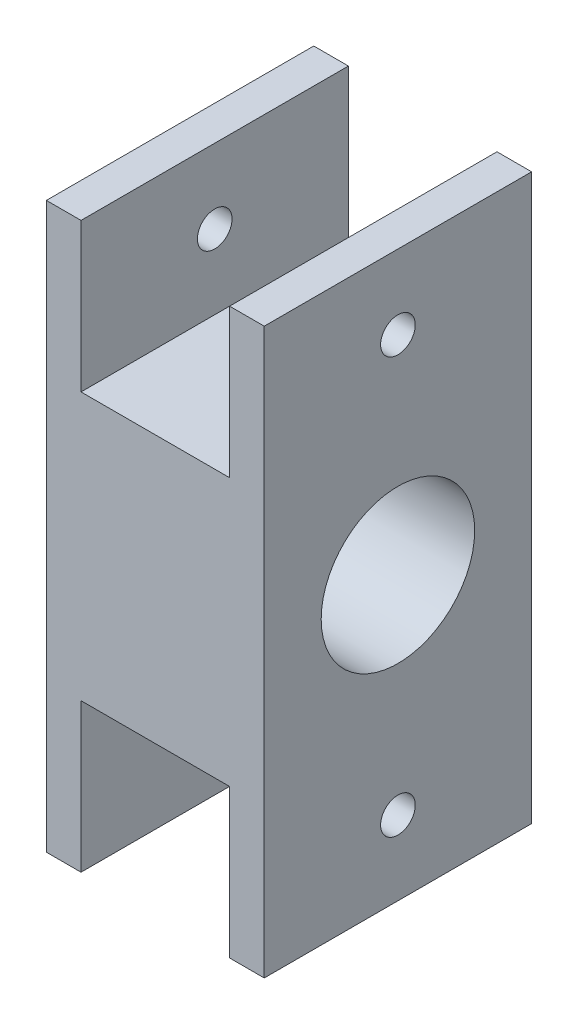
SolidWorks part; units mm, degrees
ref_plane "Front Plane" through (0, 0, 0) normal (0, 0, 1) x (1, 0, 0)
ref_plane "Top Plane" through (0, 0, 0) normal (0, 1, 0) x (1, 0, 0)
ref_plane "Right Plane" through (0, 0, 0) normal (1, 0, 0) x (0, 0, -1)
sketch "Sketch1" plane through (0, 0, 0) normal (0, 0, 1) x (1, 0, 0)
  line L0 (0, -1426.5537) -> (0, 69901.1317) construction
  line L1 (0, 0) -> (71327.6854, 0) construction
  line L2 (-22, 57) -> (-15, 57)
  line L3 (-15, 57) -> (-15, 27)
  line L4 (-15, 27) -> (15, 27)
  line L5 (15, 27) -> (15, 57)
  line L6 (15, 57) -> (22, 57)
  line L7 (22, 57) -> (22, -57)
  line L8 (22, -57) -> (15, -57)
  line L9 (15, -57) -> (15, -27)
  line L10 (15, -27) -> (-15, -27)
  line L11 (-15, -27) -> (-15, -57)
  line L12 (-15, -57) -> (-22, -57)
  line L13 (-22, -57) -> (-22, 57)
  point P9 (0, -27)
  point P18 (0, 27)
  point P19 (22, 0)
  point P20 (-22, 0)
  dimension "D1" = 30
  dimension "D2" = 7
  dimension "D3" = 54
extrude "Boss-Extrude1" add sketch "Sketch1" along normal blind 54
sketch "Sketch2" plane through (-22, 0, 0) normal (-1, 0, 0) x (0, 0, 1)
  line L0 (54, -57) -> (0, -57) construction
  line L1 (54, 57) -> (54, -57) construction
  line L2 (0, 57) -> (0, -57) construction
  line L3 (54, 57) -> (0, 57) construction
  line L4 (54, -57) -> (0, -57) construction
  line L5 (54, 57) -> (54, -57) construction
  line L6 (0, 57) -> (0, -57) construction
  line L7 (54, 57) -> (0, 57) construction
  line L8 (27, 57) -> (27, -57) construction
  line L9 (0, 42) -> (54, 42) construction
  line L10 (0, -42) -> (54, -42) construction
  point P10 (27, -42)
  point P11 (27, 42)
  dimension "D1" = 15
  dimension "D2" = 15
hole_wizard "Hole1" positions "Sketch2" profile "Sketch3" legacy end condition through all
sketch "Sketch3" plane through (-22, 42, 27) normal (0, 1, 0) x (0, 0, 1)
  line L0 (0, 0) -> (0, 44)
  line L1 (0, 44) -> (3.5, 44)
  line L2 (3.5, 44) -> (3.5, 0)
  line L3 (3.5, 0) -> (0, 0)
  line L4 (0, 110) -> (0, -10) construction
  dimension "Diameter" = 7
  dimension "Depth" = 44
sketch "Sketch4" plane through (-22, 0, 0) normal (-1, 0, 0) x (0, 0, 1)
  line L0 (0, 0) -> (54, 0) construction
  line L1 (54, 57) -> (54, -57) construction
  line L2 (27, 57) -> (27, -57) construction
  line L3 (54, 57) -> (0, 57) construction
  line L4 (54, -57) -> (0, -57) construction
  point P11 (27, 0)
hole_wizard "Hole2" positions "Sketch4" profile "Sketch5" legacy end condition through all
sketch "Sketch5" plane through (-22, 0, 27) normal (0, 1, 0) x (0, 0, 1)
  line L0 (0, 0) -> (0, 44)
  line L1 (0, 44) -> (15.5, 44)
  line L2 (15.5, 44) -> (15.5, 12)
  line L3 (15.5, 12) -> (20, 12)
  line L4 (20, 12) -> (20, 0)
  line L5 (20, 0) -> (0, 0)
  line L6 (0, 110) -> (0, -10) construction
  dimension "Depth" = 44
  dimension "Diameter" = 31
  dimension "C-Bore Diameter" = 40
  dimension "C-Bore Depth" = 12
equation "\"t_wall\"= 7mm"
equation "\"d_bearing\"= 40mm"
equation "\"w_extrusion\"= 30mm"
equation "\"D1@Sketch1\"=\"w_extrusion\""
equation "\"D2@Sketch1\"=\"t_wall\""
equation "\"D3@Sketch1\"=\"d_bearing\" +\"t_wall\" * 2"
equation "\"D1@Boss-Extrude1\"=\"d_bearing\"+\"t_wall\" *2"
equation "\"d_mount\"= 7mm"
equation "\"D1@Sketch2\"=\"w_extrusion\"/2"
equation "\"D2@Sketch2\"=\"w_extrusion\"/2"
equation "\"Diameter@Sketch3\"=\"d_mount\""
equation "\"h_bearing\"= 12mm"
equation "\"C-Bore Diameter@Sketch5\"=\"d_bearing\""
equation "\"d_flange\"= 31mm"
equation "\"Diameter@Sketch5\"=\"d_flange\""
equation "\"C-Bore Depth@Sketch5\"=\"h_bearing\""
equation "\"d_shaft\"= 17mm"
